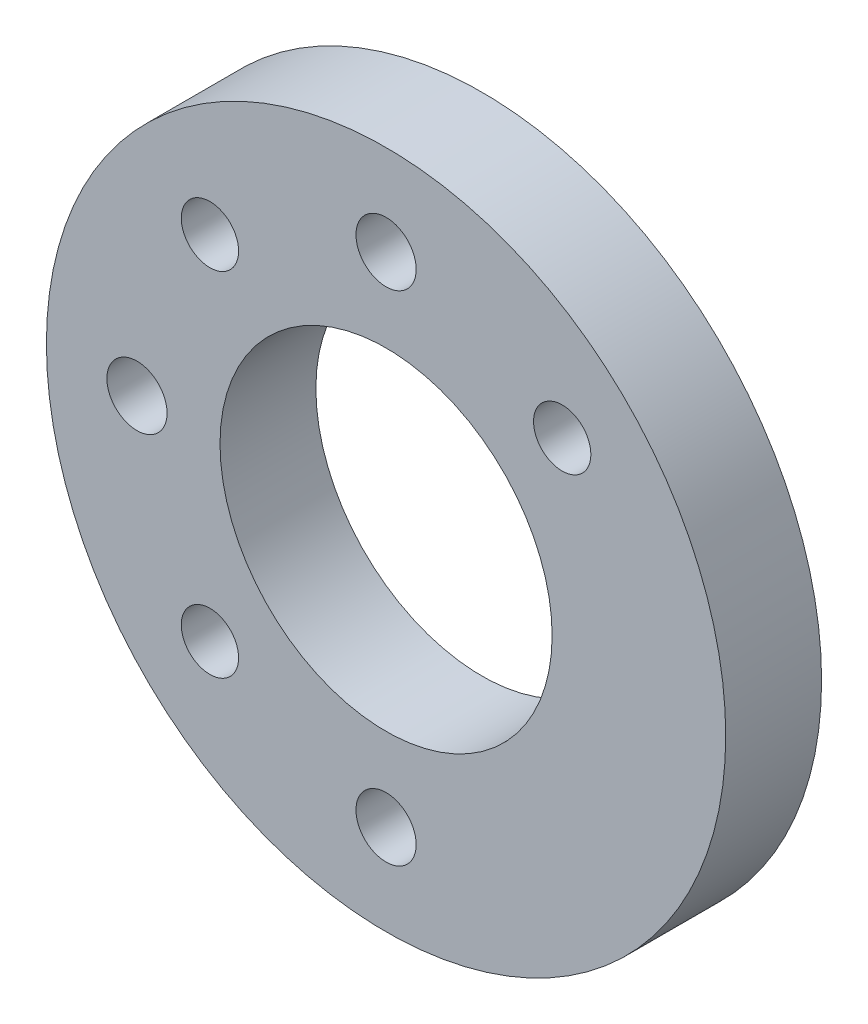
SolidWorks part; units mm, degrees
material "Balsa"
ref_plane "Front Plane" through (0, 0, 0) normal (0, 0, 1) x (1, 0, 0)
ref_plane "Top Plane" through (0, 0, 0) normal (0, 1, 0) x (1, 0, 0)
ref_plane "Right Plane" through (0, 0, 0) normal (1, 0, 0) x (0, 0, -1)
sketch "Sketch1" plane through (0, 0, 0) normal (0, 0, 1) x (1, 0, 0)
  circle A0 centre (0, 0) radius 22.5
  circle A1 centre (0, 0) radius 11
  circle A2 centre (0, 0) radius 16.5 construction
  circle A3 centre (0, 16.5) radius 1.9939
  circle A4 centre (11.6673, 11.6673) radius 1.8986
  circle A5 centre (16.5, 0) radius 1.9939 construction
  circle A6 centre (11.6673, -11.6673) radius 1.8986 construction
  circle A7 centre (0, -16.5) radius 1.9939
  circle A8 centre (-11.6673, -11.6673) radius 1.8986
  circle A9 centre (-16.5, 0) radius 1.9939
  circle A10 centre (-11.6673, 11.6673) radius 1.8986
  dimension "D1" = 45
  dimension "D2" = 22
  dimension "D3" = 33
  dimension "D4" = 3.9878
  dimension "D5" = 3.7973
  dimension "D6" = 45
  dimension "D7" = 4
extrude "Boss-Extrude1" add sketch "Sketch1" along normal blind 6.35
other "Move Face1" [suppressed] parameters "D1"=0.08
chamfer "Chamfer1" distance 2.301 angle 41 3 edges at (-9.7686, -11.6673, 0) (-9.7686, 11.6673, 0) (13.5659, 11.6673, 0)
